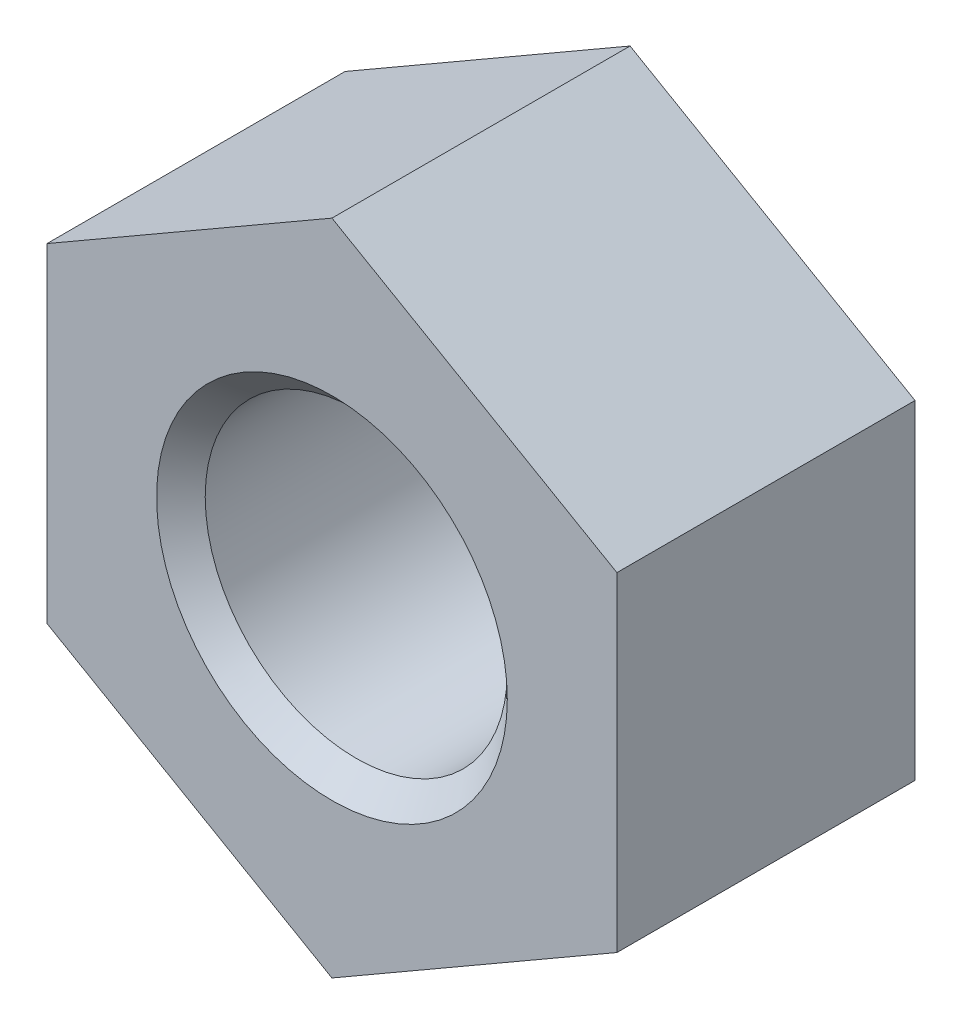
SolidWorks part; units mm, degrees
material "Сталь"
ref_plane "Спереди" through (0, 0, 0) normal (0, 0, 1) x (1, 0, 0)
ref_plane "Сверху" through (0, 0, 0) normal (0, 1, 0) x (1, 0, 0)
ref_plane "Справа" through (0, 0, 0) normal (1, 0, 0) x (0, 0, -1)
sketch "Эскиз1" plane through (0, 0, 0) normal (0, 0, 1) x (1, 0, 0)
  line L1 (0, 7.5056) -> (-6.5, 3.7528)
  line L2 (-6.5, 3.7528) -> (-6.5, -3.7528)
  line L3 (-6.5, -3.7528) -> (0, -7.5056)
  line L4 (0, -7.5056) -> (6.5, -3.7528)
  line L5 (6.5, -3.7528) -> (6.5, 3.7528)
  line L6 (6.5, 3.7528) -> (0, 7.5056)
  circle A0 centre (0, 0) radius 6.5 construction
  circle A1 centre (0, 0) radius 3.4455
  dimension "D2" = 6.891
  dimension "D1" = 13
extrude "Бобышка-Вытянуть1" add sketch "Эскиз1" along normal blind 6.8
cosmetic thread "Условное изображение резьбы1" parameters "D2"=8
chamfer "Фаска1" distance 0.5545 angle 45 2 edges at (3.4455, 0, 0) (3.4455, 0, 6.8)
